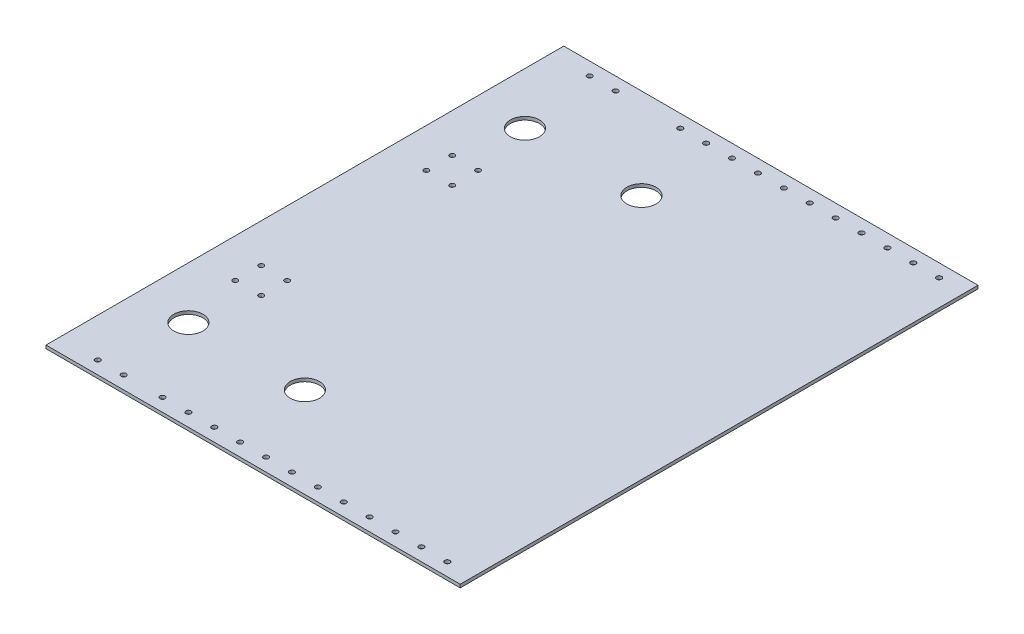
SolidWorks part; units mm, degrees
material "Lexan"
ref_plane "Front Plane" through (0, 0, 0) normal (0, 0, 1) x (1, 0, 0)
ref_plane "Top Plane" through (0, 0, 0) normal (0, 1, 0) x (1, 0, 0)
ref_plane "Right Plane" through (0, 0, 0) normal (1, 0, 0) x (0, 0, -1)
sketch "Sketch1" plane through (0, 0, 0) normal (0, 1, 0) x (1, 0, 0)
  line L1 (0, 0) -> (406.4, 0)
  line L2 (0, 0) -> (0, 508)
  line L3 (0, 508) -> (406.4, 508)
  line L4 (406.4, 0) -> (406.4, 508)
  dimension "D1" = 406.4
  dimension "D2" = 508
extrude "Boss-Extrude1" add sketch "Sketch1" along normal blind 3.175
sketch "Sketch2" plane through (0, 3.175, 0) normal (0, 1, 0) x (1, 0, 0)
  line L0 (107.95, 419.1) -> (107.95, 508) construction
  line L1 (50.8, 419.1) -> (165.1, 419.1) construction
  line L2 (406.4, 0) -> (406.4, 508) construction
  line L3 (50.8, 88.9) -> (165.1, 88.9) construction
  line L5 (406.4, 508) -> (0, 508) construction
  line L6 (107.95, 88.9) -> (107.95, 0) construction
  line L7 (0, 0) -> (406.4, 0) construction
  circle A0 centre (50.8, 419.1) radius 14.2875
  circle A1 centre (165.1, 419.1) radius 14.2875
  circle A2 centre (50.8, 88.9) radius 14.2875
  circle A3 centre (165.1, 88.9) radius 14.2875
  dimension "D1" = 28.575
  dimension "D2" = 28.575
  dimension "D3" = 28.575
  dimension "D4" = 28.575
  dimension "D5" = 114.3
  dimension "D6" = 114.3
  dimension "D7" = 330.2
  dimension "D9" = 241.3
extrude "Cut-Extrude1" cut sketch "Sketch2" against normal blind 3.175
sketch "Sketch3" plane through (0, 3.175, 0) normal (0, 1, 0) x (1, 0, 0)
  line L0 (0, 12.7) -> (406.4, 12.7) construction
  line L1 (0, 508) -> (0, 0) construction
  line L2 (406.4, 0) -> (406.4, 508) construction
  line L3 (0, 0) -> (406.4, 0) construction
  line L4 (101.6, 0) -> (101.6, 12.7) construction
  line L5 (0, 254) -> (406.4, 254) construction
  line L6 (101.6, 508) -> (101.6, 495.3) construction
  line L7 (0, 495.3) -> (406.4, 495.3) construction
  circle A0 centre (38.1, 12.7) radius 2.4892
  circle A1 centre (63.5, 12.7) radius 2.4892
  circle A2 centre (127, 12.7) radius 2.4892
  circle A3 centre (152.4, 12.7) radius 2.4892
  circle A4 centre (177.8, 12.7) radius 2.4892
  circle A5 centre (203.2, 12.7) radius 2.4892
  circle A6 centre (228.6, 12.7) radius 2.4892
  circle A7 centre (254, 12.7) radius 2.4892
  circle A8 centre (279.4, 12.7) radius 2.4892
  circle A9 centre (304.8, 12.7) radius 2.4892
  circle A10 centre (330.2, 12.7) radius 2.4892
  circle A11 centre (355.6, 12.7) radius 2.4892
  circle A12 centre (381, 12.7) radius 2.4892
  circle A13 centre (381, 495.3) radius 2.4892
  circle A14 centre (355.6, 495.3) radius 2.4892
  circle A15 centre (330.2, 495.3) radius 2.4892
  circle A16 centre (304.8, 495.3) radius 2.4892
  circle A17 centre (279.4, 495.3) radius 2.4892
  circle A18 centre (254, 495.3) radius 2.4892
  circle A19 centre (228.6, 495.3) radius 2.4892
  circle A20 centre (203.2, 495.3) radius 2.4892
  circle A21 centre (177.8, 495.3) radius 2.4892
  circle A22 centre (152.4, 495.3) radius 2.4892
  circle A23 centre (127, 495.3) radius 2.4892
  circle A24 centre (63.5, 495.3) radius 2.4892
  circle A25 centre (38.1, 495.3) radius 2.4892
  circle A27 centre (101.6, 12.7) radius 2.4892
  dimension "D1" = 4.9784
  dimension "D2" = 38.1
  dimension "D4" = 25.4
  dimension "D6" = 25.4
  dimension "D7" = 11
  dimension "D3" = 12.7
  dimension "D5" = 38.1
extrude "Cut-Extrude2" cut sketch "Sketch3" against normal through all both and the other way through all
sketch "Sketch4" plane through (0, 0, 0) normal (0, -1, 0) x (1, 0, 0)
  circle A0 centre (38.1796, -334.9387) radius 2.413
  circle A1 centre (63.5796, -334.9387) radius 2.413
  circle A2 centre (63.5796, -360.3387) radius 2.413
  circle A3 centre (38.1796, -360.3387) radius 2.413
  circle A4 centre (63.4615, -173.0601) radius 2.413
  circle A5 centre (38.0615, -173.0601) radius 2.413
  circle A6 centre (38.0615, -147.6601) radius 2.413
  circle A7 centre (63.4615, -147.6601) radius 2.413
extrude "Cut-Extrude3" cut sketch "Sketch4" against normal through all both
